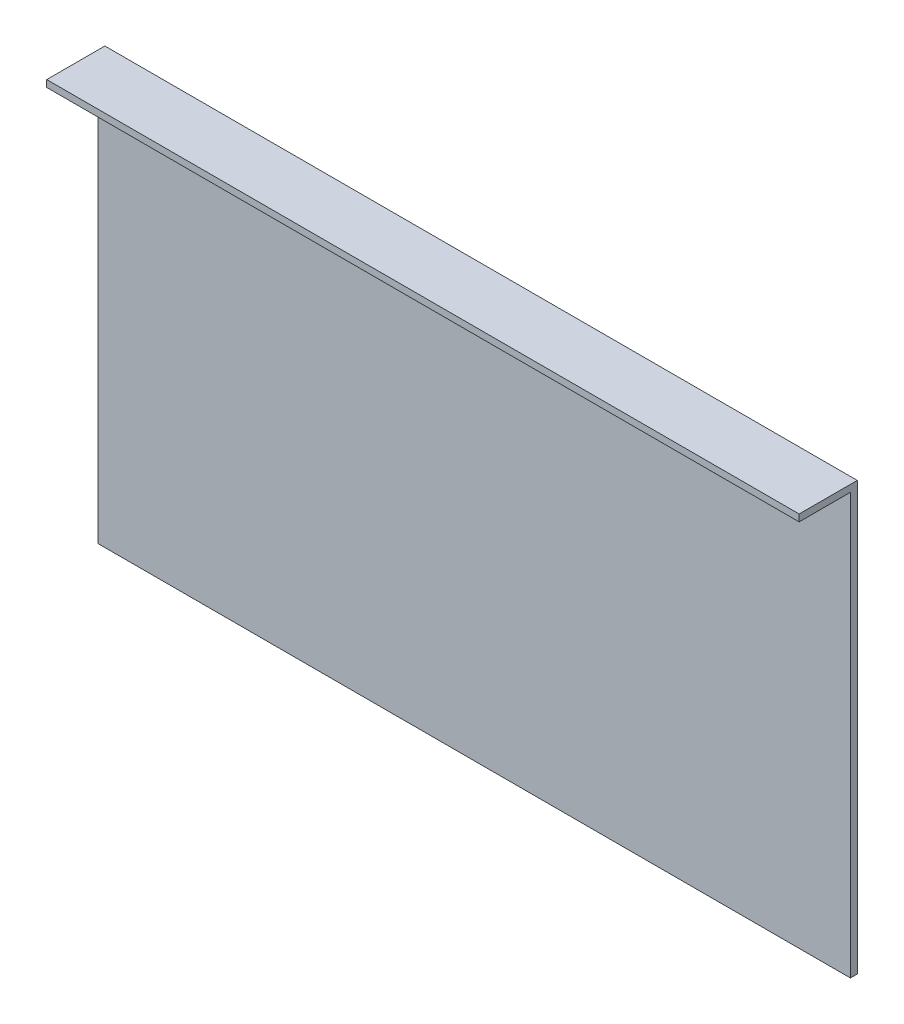
SolidWorks part; units mm, degrees
material "6061-T6 (SS)"
ref_plane "Front Plane" through (0, 0, 0) normal (0, 0, 1) x (1, 0, 0)
ref_plane "Top Plane" through (0, 0, 0) normal (0, 1, 0) x (1, 0, 0)
ref_plane "Right Plane" through (0, 0, 0) normal (1, 0, 0) x (0, 0, -1)
sketch "Sketch1" plane through (0, 0, 0) normal (0, 0, 1) x (1, 0, 0)
  line L1 (0, 0) -> (440, 0)
  line L2 (0, 0) -> (0, 250)
  line L3 (0, 250) -> (440, 250)
  line L4 (440, 0) -> (440, 250)
  dimension "D1" = 250
  dimension "D2" = 440
extrude "Boss-Extrude1" add sketch "Sketch1" along normal blind 4
sketch "Sketch2" plane through (0, 0, 4) normal (0, 0, 1) x (1, 0, 0)
  line L0 (440, 0) -> (440, 250) construction
  line L1 (0, 250) -> (440, 250)
  line L2 (0, 250) -> (0, 246)
  line L3 (0, 246) -> (440, 246)
  line L4 (440, 250) -> (440, 246)
  dimension "D1" = 4
extrude "Boss-Extrude2" add sketch "Sketch2" along normal blind 30
